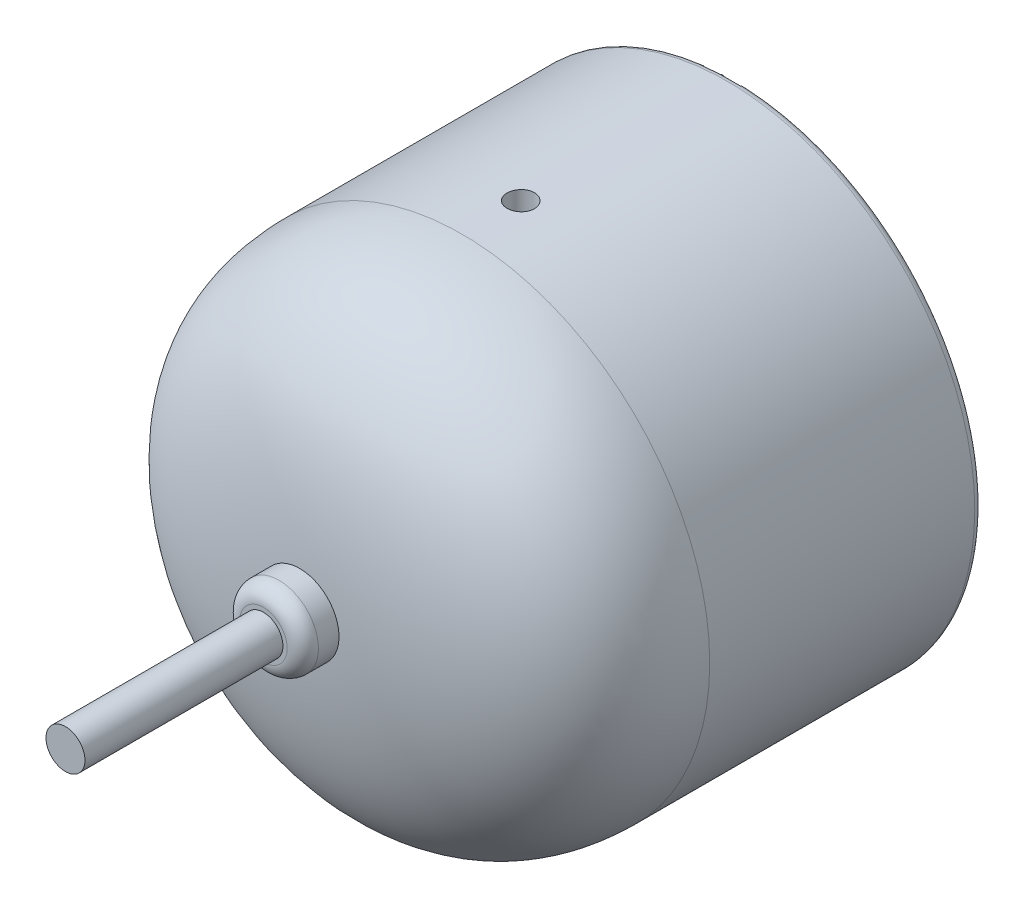
SolidWorks part; units mm, degrees
ref_plane "Front Plane" through (0, 0, 0) normal (0, 0, 1) x (1, 0, 0)
ref_plane "Top Plane" through (0, 0, 0) normal (0, 1, 0) x (1, 0, 0)
ref_plane "Right Plane" through (0, 0, 0) normal (1, 0, 0) x (0, 0, -1)
sketch "Sketch3" plane through (0, 0, 0) normal (0, 1, 0) x (1, 0, 0)
  line L0 (0, 25.32) -> (27.625, 25.32)
  line L1 (27.625, 25.32) -> (27.625, 26.5)
  line L2 (28.625, 27.5) -> (30.75, 27.5)
  line L3 (31.75, 26.5) -> (31.75, -7.5)
  line L4 (0, -28.5) -> (0, 25.32)
  line L5 (0, 65.3333) -> (0, -39.4699) construction
  line L6 (25.7862, -28.5) -> (-25.7862, -28.5) construction
  line L7 (31.75, 21.2518) -> (31.75, -13.1835) construction
  arc A0 (27.625, 26.5) -> (28.625, 27.5) centre (28.625, 26.5) cw
  arc A1 (30.75, 27.5) -> (31.75, 26.5) centre (30.75, 26.5) cw
  spline S0 degree 3 poles (0, -28.5) (23.2956, -28.5) (31.75, -20.2065) (31.75, -7.5) knots 0 0 0 0 1 1 1 1
  dimension "D7" = 1
  dimension "D1" = 56
  dimension "D2" = 55.25
  dimension "D3" = 63.5
  dimension "D4" = 2.18
  dimension "D5" = 27.5
  dimension "D6" = 35
revolve "Revolve1" add sketch "Sketch3" angle 360 about L5
sketch "Sketch6" plane through (0, 0, 0) normal (0, 1, 0) x (1, 0, 0)
  circle A0 centre (0, 0) radius 1.75
  dimension "D1" = 3.5
extrude "Cut-Extrude1" cut sketch "Sketch6" against normal through all from offset 27 offset against normal yes
mirror "Mirror1" about plane through (0, 0, 0) normal (0, 1, 0) of "Cut-Extrude1"
ref_plane "Plane1" through (0, 0, 25) normal (0, 0, 1) x (1, 0, 0)
sketch "Sketch7" plane through (0, 0, 25) normal (0, 0, 1) x (1, 0, 0)
  circle A0 centre (0, 0) radius 5.05
  dimension "D1" = 10.1
extrude "Boss-Extrude2" add sketch "Sketch7" along normal blind 8
fillet "Fillet1" radius 2 1 edges at (5.05, 0, 33)
sketch "Sketch8" plane through (0, 0, 33) normal (0, 0, 1) x (1, 0, 0)
  circle A0 centre (0, 0) radius 2.5
  dimension "D1" = 5
extrude "Boss-Extrude3" add sketch "Sketch8" along normal blind 25.4
